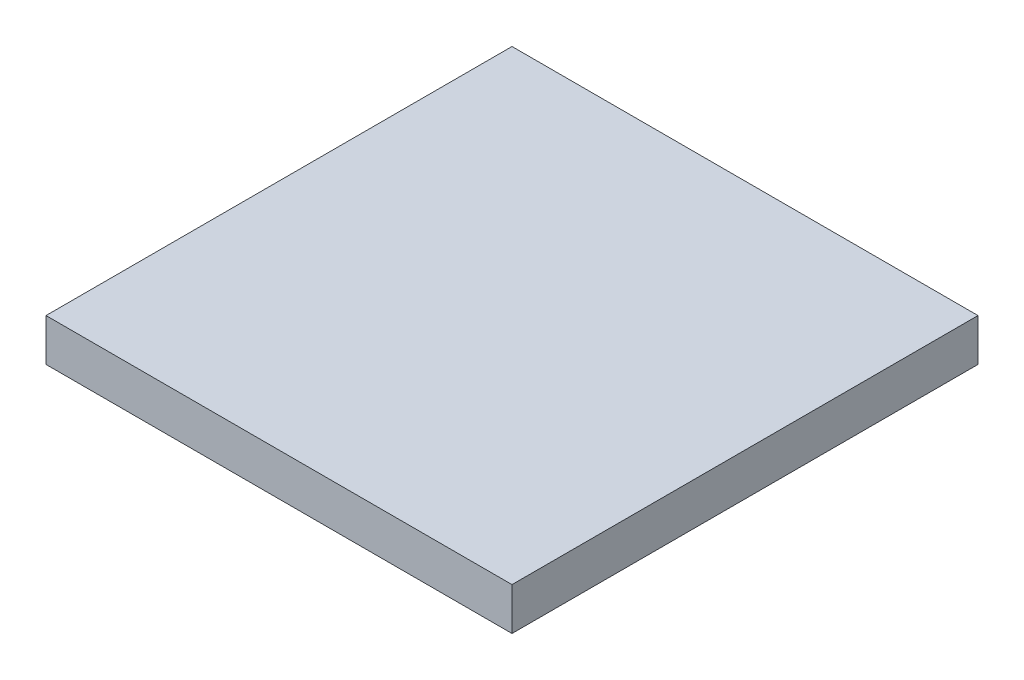
SolidWorks part; units mm, degrees
ref_plane "Front Plane" through (0, 0, 0) normal (0, 0, 1) x (1, 0, 0)
ref_plane "Top Plane" through (0, 0, 0) normal (0, 1, 0) x (1, 0, 0)
ref_plane "Right Plane" through (0, 0, 0) normal (1, 0, 0) x (0, 0, -1)
sketch "Sketch2" plane through (0, 0, 0) normal (0, 1, 0) x (1, 0, 0)
  line L0 (8.25, 0) -> (-8.25, 0)
  line L1 (-8.25, 0) -> (-8.25, -16.5)
  line L2 (-8.25, -16.5) -> (8.25, -16.5)
  line L3 (8.25, -16.5) -> (8.25, 0)
  point P3 (0, 0)
  dimension "D1" = 16.5
extrude "Boss-Extrude1" add sketch "Sketch2" along normal blind 1.5
